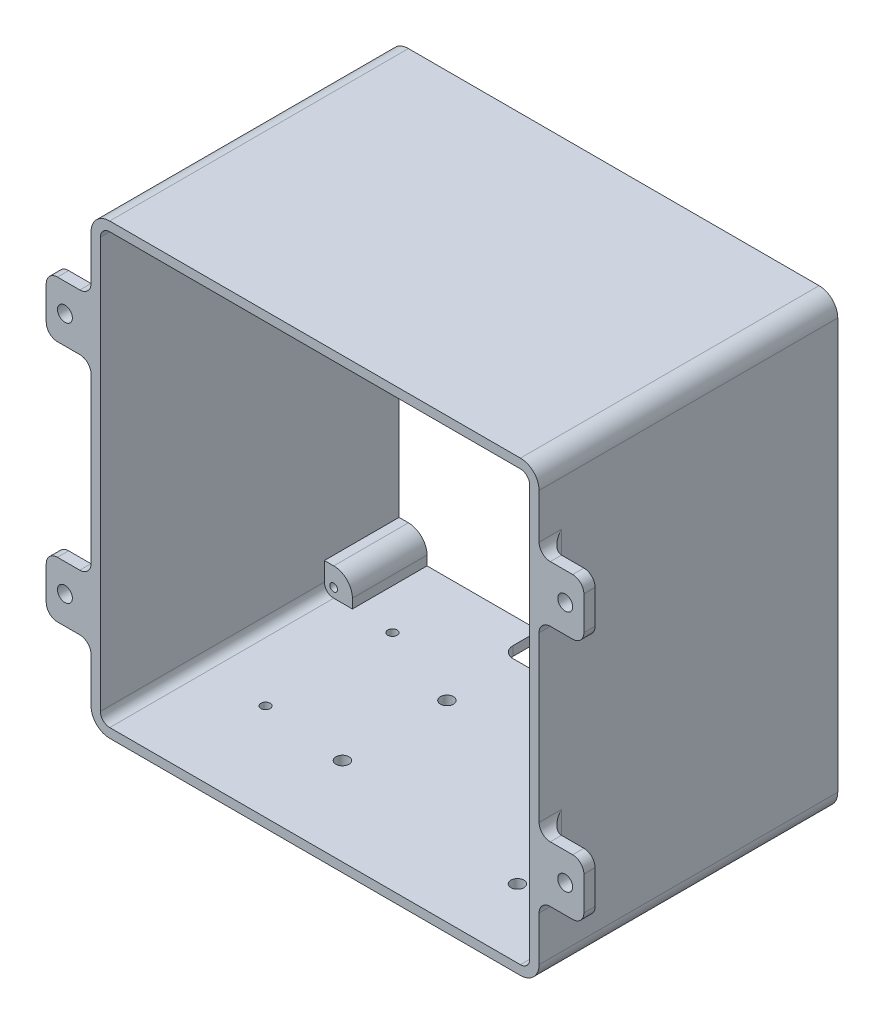
SolidWorks part; units mm, degrees
ref_plane "Front Plane" through (0, 0, 0) normal (0, 0, 1) x (1, 0, 0)
ref_plane "Top Plane" through (0, 0, 0) normal (0, 1, 0) x (1, 0, 0)
ref_plane "Right Plane" through (0, 0, 0) normal (1, 0, 0) x (0, 0, -1)
sketch "Sketch1" plane through (0, 0, 0) normal (0, 0, 1) x (1, 0, 0)
  line L4 (29, 86) -> (-81, 86)
  line L5 (-86, 81) -> (-86, -29)
  line L6 (-81, -34) -> (29, -34)
  line L7 (34, -29) -> (34, 81)
  line L8 (29, 86) -> (-81, 86)
  line L9 (-86, 81) -> (-86, -29)
  line L10 (-81, -34) -> (29, -34)
  line L11 (34, -29) -> (34, 81)
  arc A4 (-81, 86) -> (-86, 81) centre (-81, 81) ccw
  arc A5 (-86, -29) -> (-81, -34) centre (-81, -29) ccw
  arc A6 (29, -34) -> (34, -29) centre (29, -29) ccw
  arc A7 (34, 81) -> (29, 86) centre (29, 81) ccw
  arc A8 (-81, 86) -> (-86, 81) centre (-81, 81) ccw
  arc A9 (-86, -29) -> (-81, -34) centre (-81, -29) ccw
  arc A10 (29, -34) -> (34, -29) centre (29, -29) ccw
  arc A11 (34, 81) -> (29, 86) centre (29, 81) ccw
  dimension "D1" = 0
extrude "Extrude-Thin1" add sketch "Sketch1" along normal blind 80 thin thin type one direction reverse wall 2.5
sketch "Sketch2" plane through (0, 0, 0) normal (0, 0, 1) x (1, 0, 0)
  line L0 (29, -24) -> (31.5, -24)
  line L1 (-76, -29) -> (-76, -31.5)
  line L2 (31.5, -29) -> (31.5, 81) construction
  line L3 (-76, -31.5) -> (-81, -31.5)
  line L4 (31.5, -24) -> (31.5, -29)
  line L5 (29, -31.5) -> (24, -31.5)
  line L6 (-81, -31.5) -> (29, -31.5) construction
  line L7 (24, -31.5) -> (24, -29)
  line L8 (31.5, 26) -> (-83.5, 26) construction
  line L9 (-83.5, 81) -> (-83.5, -29) construction
  line L10 (-83.5, -29) -> (-83.5, -24)
  line L11 (-83.5, -24) -> (-81, -24)
  line L12 (-81, 76) -> (-83.5, 76)
  line L13 (-83.5, 76) -> (-83.5, 81)
  line L14 (-81, 83.5) -> (-76, 83.5)
  line L15 (-76, 83.5) -> (-76, 81)
  line L16 (24, 81) -> (24, 83.5)
  line L17 (24, 83.5) -> (29, 83.5)
  line L18 (31.5, 81) -> (31.5, 76)
  line L19 (31.5, 76) -> (29, 76)
  arc A0 (29, -24) -> (24, -29) centre (29, -29) ccw
  arc A1 (31.5, -29) -> (29, -31.5) centre (29, -29) cw
  arc A2 (-76, -29) -> (-81, -24) centre (-81, -29) ccw
  arc A3 (-81, -31.5) -> (-83.5, -29) centre (-81, -29) cw
  arc A4 (-81, 76) -> (-76, 81) centre (-81, 81) ccw
  arc A5 (-83.5, 81) -> (-81, 83.5) centre (-81, 81) cw
  arc A6 (24, 81) -> (29, 76) centre (29, 81) ccw
  arc A7 (29, 83.5) -> (31.5, 81) centre (29, 81) cw
  point P19 (-26, 26)
  point P46 (-26, 26)
  dimension "D1" = 5
  dimension "D2" = 4
extrude "Boss-Extrude2" add sketch "Sketch2" along normal blind 20
sketch "Sketch3" plane through (0, -34, 0) normal (0, -1, 0) x (1, 0, 0)
  circle A1 centre (9.8662, 61.6577) radius 1.75
  circle A2 centre (8.691, 13.3953) radius 1.75
  circle A5 centre (-42.1937, 56.4754) radius 1.75 construction
  circle A6 centre (-42.1937, 56.4754) radius 1.75
  circle A7 centre (-42.1389, 28.5355) radius 1.75 construction
  circle A8 centre (-42.1389, 28.5355) radius 1.75
  circle A9 centre (-65.1537, 54.1052) radius 1.25 construction
  circle A10 centre (-65.1537, 54.1052) radius 1.25
  circle A11 centre (-65.1537, 20.1052) radius 1.25 construction
  circle A12 centre (-65.1537, 20.1052) radius 1.25
  dimension "D1" = 3.5
extrude "Cut-Extrude1" cut sketch "Sketch3" against normal blind 10
sketch "Sketch4" plane through (0, -34, 0) normal (0, -1, 0) x (1, 0, 0)
  line L0 (-81, 0) -> (29, 0) construction
  line L1 (-6, 0) -> (-46, 0)
  line L2 (-6, 0) -> (-6, 7)
  line L3 (-9, 10) -> (-43, 10)
  line L4 (-46, 0) -> (-46, 7)
  line L5 (29, -2.5) -> (-81, -2.5) construction
  arc A0 (-43, 10) -> (-46, 7) centre (-43, 7) ccw
  arc A1 (-6, 7) -> (-9, 10) centre (-9, 7) ccw
  point P6 (-26, 0)
  point P9 (-26, -2.5)
  point P12 (-46, 10)
  point P15 (-6, 10)
  dimension "D3" = 3
  dimension "D1" = 40
  dimension "D2" = 10
extrude "Cut-Extrude2" cut sketch "Sketch4" against normal up to next
sketch "Sketch6" plane through (0, 0, 80) normal (0, 0, 1) x (1, 0, 0)
  line L0 (-86, 81) -> (-86, -29) construction
  line L1 (-86, 66) -> (-95, 66)
  line L2 (-86, 66) -> (-86, 51)
  line L3 (-86, 51) -> (-95, 51)
  line L4 (-98, 63) -> (-98, 54)
  line L5 (-83.5, 26) -> (31.5, 26) construction
  line L14 (29, 86) -> (-81, 86) construction
  line L19 (-26, 83.5) -> (-26, -31.5) construction
  line L20 (29, 83.5) -> (-81, 83.5) construction
  line L21 (-81, -31.5) -> (29, -31.5) construction
  line L22 (-83.5, 81) -> (-83.5, -29) construction
  line L23 (31.5, -29) -> (31.5, 81) construction
  line L24 (46, 63) -> (46, 54)
  line L25 (34, 51) -> (43, 51)
  line L26 (34, 66) -> (34, 51)
  line L27 (34, 66) -> (43, 66)
  line L28 (34, -14) -> (43, -14)
  line L29 (34, -14) -> (34, 1)
  line L30 (34, 1) -> (43, 1)
  line L31 (46, -11) -> (46, -2)
  line L32 (-98, -11) -> (-98, -2)
  line L33 (-86, 1) -> (-95, 1)
  line L34 (-86, -14) -> (-86, 1)
  line L35 (-86, -14) -> (-95, -14)
  arc A0 (-95, 66) -> (-98, 63) centre (-95, 63) ccw
  arc A1 (-95, 51) -> (-98, 54) centre (-95, 54) cw
  circle A2 centre (-93, 58.5) radius 2
  circle A3 centre (41, 58.5) radius 2
  arc A4 (43, 51) -> (46, 54) centre (43, 54) ccw
  arc A5 (43, 66) -> (46, 63) centre (43, 63) cw
  arc A6 (43, -14) -> (46, -11) centre (43, -11) ccw
  arc A7 (43, 1) -> (46, -2) centre (43, -2) cw
  circle A8 centre (41, -6.5) radius 2
  circle A9 centre (-93, -6.5) radius 2
  arc A10 (-95, 1) -> (-98, -2) centre (-95, -2) ccw
  arc A11 (-95, -14) -> (-98, -11) centre (-95, -11) cw
  point P10 (-98, 66)
  point P13 (-98, 51)
  point P18 (-26, 26)
  point P21 (-86, 58.5)
  point P40 (46, 51)
  point P41 (46, 66)
  point P52 (46, -14)
  point P53 (46, 1)
  point P64 (-98, 1)
  point P65 (-98, -14)
  line M18 (-86, 81) -> (-86, -29)
  line M22 (34, -29) -> (34, 81)
  dimension "D3" = 3
  dimension "D4" = 4
  dimension "D1" = 15
  dimension "D2" = 12
  dimension "D5" = 20
  dimension "D6" = 5
extrude "Boss-Extrude3" add sketch "Sketch6" against normal blind 3 contours A11 L35 L33 A10 L32 A9 M18 | A7 L30 L28 A6 L31 A8 M22 | A5 L27 L25 A4 L24 A3 M22 | A1 L3 L1 A0 L4 A2 M18
fillet "Fillet1" radius 3 8 edges at (-86, 51, 78.5) (-86, 66, 78.5) (-86, 1, 78.5) (-86, -14, 78.5) (34, -14, 78.5) (34, 1, 78.5) (34, 66, 78.5) (34, 51, 78.5)
fillet "Fillet2" radius 3 4 edges at (34, 58.5, 77) (34, -6.5, 77) (-86, 58.5, 77) (-86, -6.5, 77)
hole_wizard "Tap Drill for M2.5x0.45 Tap1" positions "Sketch11" profile "Sketch12" hole size "M2.5x0.45" standard "ANSI Metric" end condition through all
sketch "Sketch11" plane through (0, 0, 0) normal (0, 0, -1) x (-1, 0, 0)
  point P0 (81, -29)
  point P3 (81, 81)
  point P6 (-29, -29)
  point P9 (-29, 81)
sketch "Sketch12" plane through (-81, -29, 0) normal (1, 0, 0) x (0, 1, 0)
  line L0 (0, 0) -> (0, 80)
  line L1 (0, 80) -> (1.025, 80)
  line L2 (1.025, 80) -> (1.025, 0)
  line L5 (1.025, 0) -> (0, 0)
  line L11 (0, -6.35) -> (0, 107.95) construction
  dimension "Thru Hole Dia." = 2.05
  dimension "Thru Hole Depth" = 80
